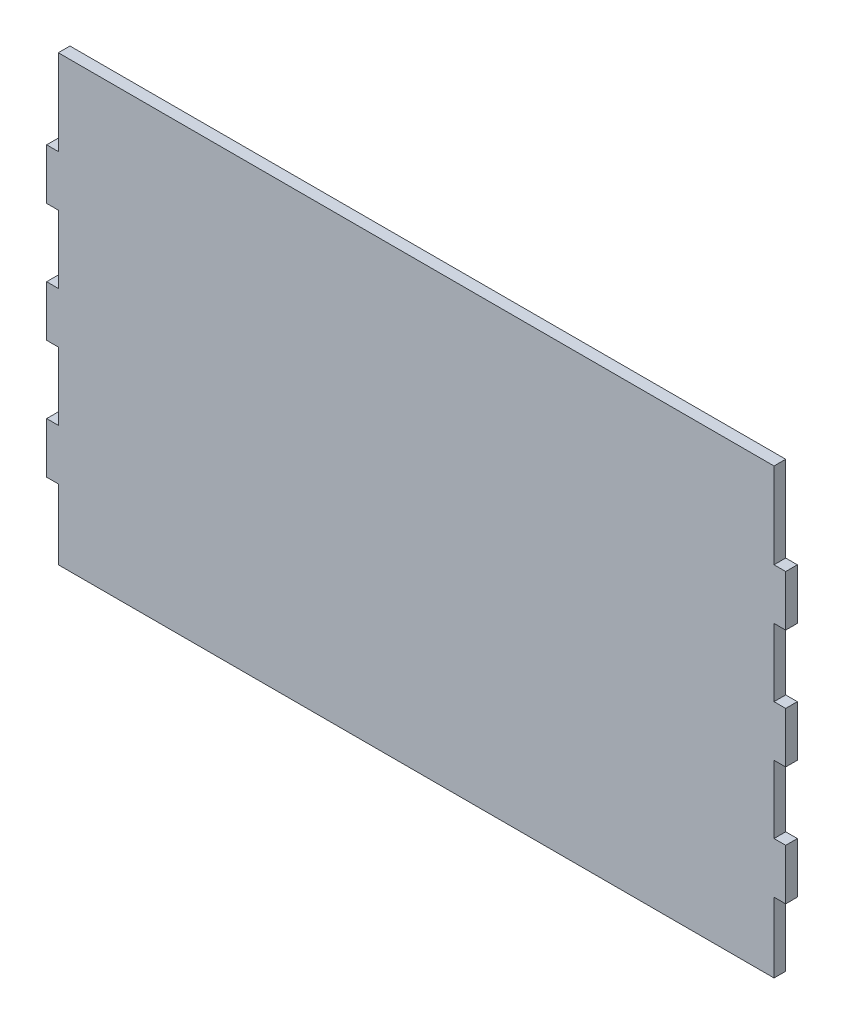
SolidWorks part; units mm, degrees
ref_plane "Front Plane" through (0, 0, 0) normal (0, 0, 1) x (1, 0, 0)
ref_plane "Top Plane" through (0, 0, 0) normal (0, 1, 0) x (1, 0, 0)
ref_plane "Right Plane" through (0, 0, 0) normal (1, 0, 0) x (0, 0, -1)
sketch "Croquis1" plane through (0, 0, 0) normal (0, 0, 1) x (1, 0, 0)
  line L1 (-95, 55) -> (95, 55)
  line L2 (-95, 55) -> (-95, -55)
  line L3 (-95, -55) -> (95, -55)
  line L4 (95, 55) -> (95, -55)
  line L5 (-95, 55) -> (95, -55) construction
  line L6 (-95, -55) -> (95, 55) construction
  point P0 (0, 0)
  dimension "D1" = 190
  dimension "D2" = 110
extrude "Saliente-Extruir1" add sketch "Croquis1" along normal blind 3
sketch "Croquis2" plane through (0, 0, 3) normal (0, 0, 1) x (1, 0, 0)
  line L0 (-95, 55) -> (-95, -55) construction
  line L1 (-95, 37) -> (-92, 37)
  line L2 (-95, 37) -> (-95, 23.9518)
  line L3 (-95, 23.9518) -> (-92, 23.9518)
  line L6 (-95, 6.5241) -> (-95, -6.5241)
  line L8 (-95, 6.5241) -> (-92, 6.5241)
  line L10 (-95, -6.5241) -> (-92, -6.5241)
  line L11 (-95, -23.9518) -> (-95, -37)
  line L12 (-95, -23.9518) -> (-92, -23.9518)
  line L14 (-95, -37) -> (-92, -37)
  line L15 (-95, -55) -> (95, -55) construction
  line L16 (95, 55) -> (-95, 55) construction
  line L17 (0, -55) -> (0, 55) construction
  line L18 (95, -23.9518) -> (92, -23.9518)
  line L19 (-92, -52) -> (92, -52)
  line L20 (92, -52) -> (92, 52)
  line L21 (-92, 52) -> (-92, -52)
  line L22 (92, 52) -> (-92, 52)
  line L24 (92, -52) -> (92, -37)
  line L25 (-92, 52) -> (-92, 37)
  line L28 (95, -37) -> (92, -37)
  line L29 (95, -23.9518) -> (95, -37)
  line L30 (95, 6.5241) -> (92, 6.5241)
  line L32 (95, -6.5241) -> (92, -6.5241)
  line L33 (95, 6.5241) -> (95, -6.5241)
  line L34 (95, 23.9518) -> (92, 23.9518)
  line L36 (95, 37) -> (92, 37)
  line L37 (95, 37) -> (95, 23.9518)
  line L38 (-92, 23.9518) -> (-92, 6.5241)
  line L39 (-92, -6.5241) -> (-92, -23.9518)
  line L40 (-92, -37) -> (-92, -52)
  line L41 (92, -23.9518) -> (92, -6.5241)
  line L42 (92, 6.5241) -> (92, 23.9518)
  line L43 (92, 37) -> (92, 52)
  line L44 (-92, 52) -> (-92, 55)
  line L45 (92, 52) -> (92, 55)
  line L46 (-92, -52) -> (-92, -55)
  line L47 (92, -52) -> (92, -55)
  line L48 (-92, -55) -> (92, -55)
  line L49 (-92, 55) -> (92, 55)
  line M3 (95, -55) -> (95, 55)
  line M4 (95, 55) -> (-95, 55)
  line M5 (-95, 55) -> (-95, -55)
  line M6 (-95, -55) -> (95, -55)
  dimension "D3" = 18
  dimension "D4" = 18
  dimension "D1" = 3
  dimension "D2" = 3
extrude "Cortar-Extruir1" cut sketch "Croquis2" against normal blind 3 contours L25 L44 L1 M4 M5 | L38 L3 L8 M5 | L45 L43 L36 M3 M4 | L42 L30 L34 M3 | L41 L18 L32 M3 | L24 L47 L28 M6 M3 | L39 L10 L12 M5 | L46 L40 L14 M5 M6
sketch "Croquis4" plane through (0, 0, 0) normal (0, 0, -1) x (-1, 0, 0)
  line L6 (92, 55) -> (92, 37) construction
  line L7 (-92, 55) -> (92, 55)
  line L8 (-92, 55) -> (-92, 59)
  line L9 (-92, 59) -> (92, 59)
  line L10 (92, 55) -> (92, 59)
  dimension "D1" = 4
extrude "Saliente-Extruir3" add sketch "Croquis4" against normal blind 3
sketch "Croquis6" plane through (0, 0, 0) normal (0, 0, -1) x (-1, 0, 0)
  line L0 (-175, -10.7078) -> (175, -10.7078) construction
  text T0 "ITAM " font "Century Gothic" height 25
  point P2 (0, -10.7078)
  dimension "D1" = 350
extrude "Cortar-Extruir4" cut sketch "Croquis6" against normal blind 1.5
